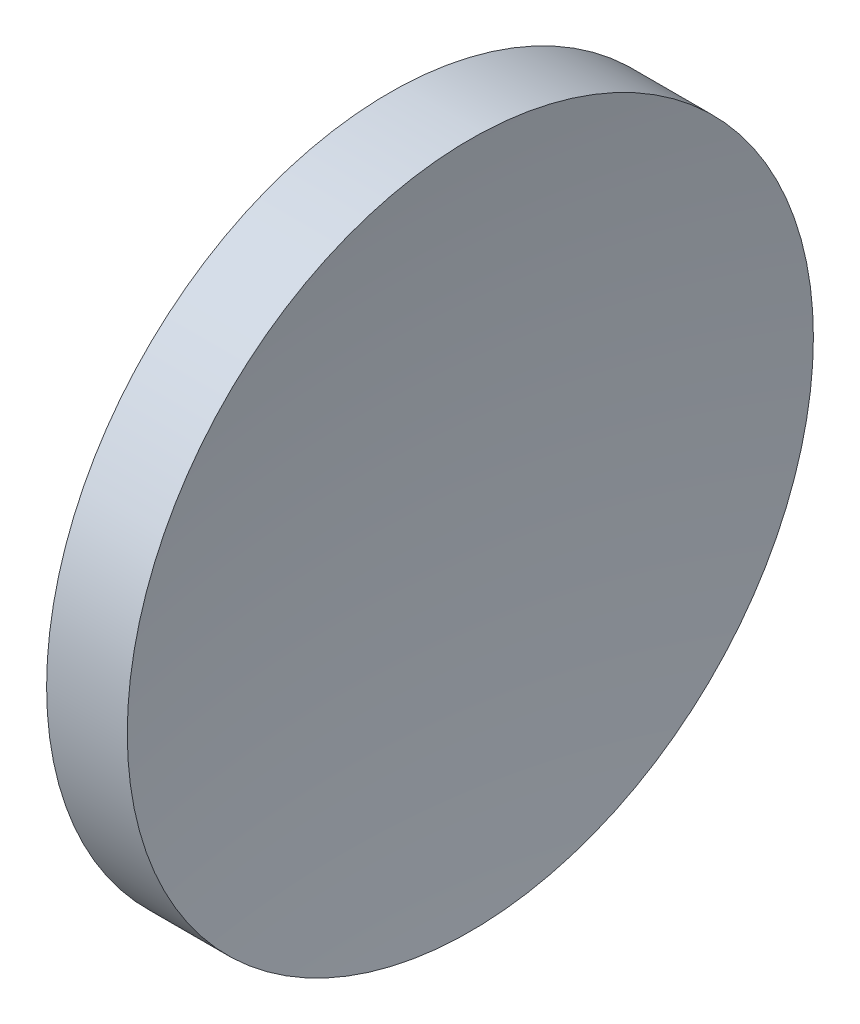
SolidWorks part; units mm, degrees
ref_plane "前视基准面" through (0, 0, 0) normal (0, 0, 1) x (1, 0, 0)
ref_plane "上视基准面" through (0, 0, 0) normal (0, 1, 0) x (1, 0, 0)
ref_plane "右视基准面" through (0, 0, 0) normal (1, 0, 0) x (0, 0, -1)
sketch "草图1" plane through (0, 0, 0) normal (0, 0, 1) x (1, 0, 0)
  line L0 (56.1009, 32.6108) -> (68.2773, 32.6108) construction
  line L1 (57.5323, 32.6108) -> (57.5323, 45.1108)
  line L2 (57.5323, 45.1108) -> (60.4714, 45.1108)
  line L3 (59.5323, 32.6108) -> (57.5323, 32.6108)
  arc A0 (60.4714, 45.1108) -> (59.5323, 32.6108) centre (142.1523, 32.6894) ccw
revolve "旋转1" add sketch "草图1" angle 360 about L0
